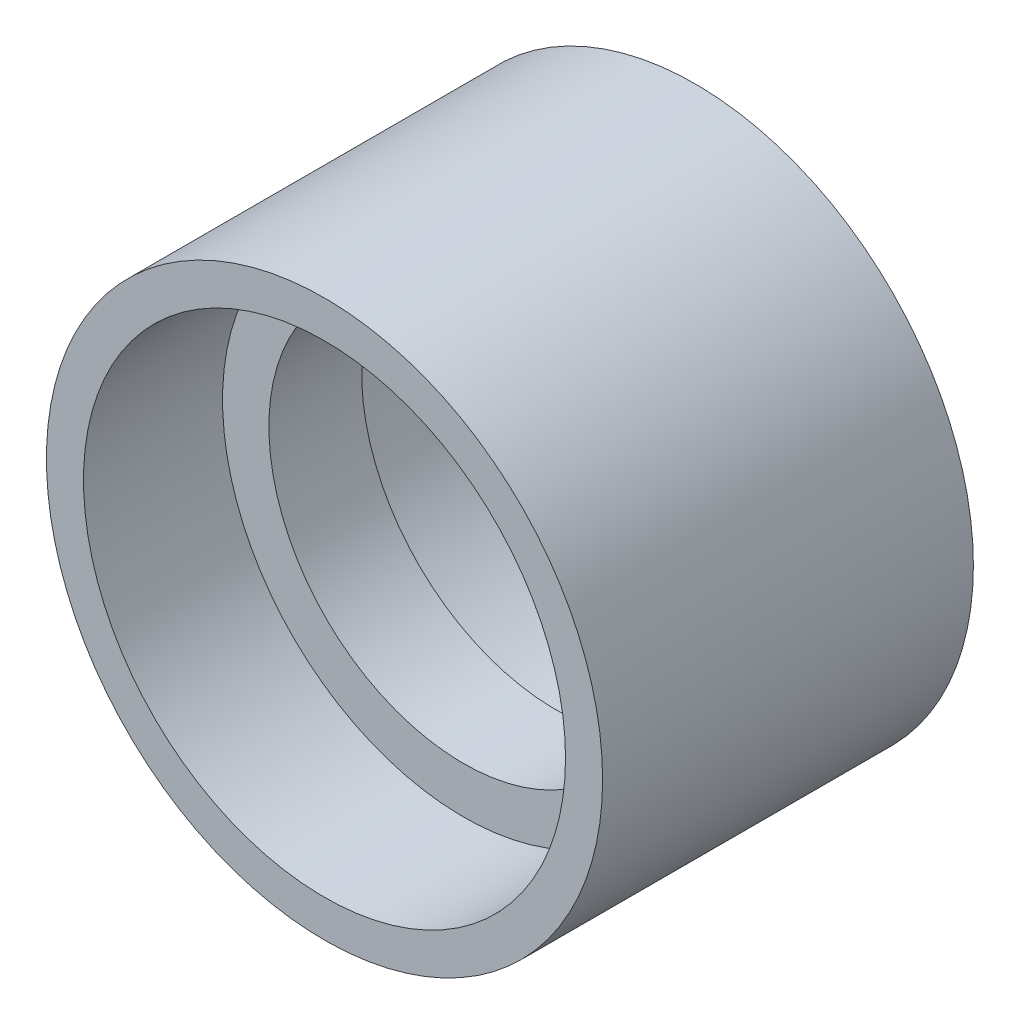
SolidWorks part; units mm, degrees
material "AISI 1020"
ref_plane "Спереди" through (0, 0, 0) normal (0, 0, 1) x (1, 0, 0)
ref_plane "Сверху" through (0, 0, 0) normal (0, 1, 0) x (1, 0, 0)
ref_plane "Справа" through (0, 0, 0) normal (1, 0, 0) x (0, 0, -1)
sketch "Эскиз1" plane through (0, 0, 0) normal (1, 0, 0) x (0, 0, -1)
  line L0 (-1000, 0) -> (49000, 0) construction
  line L1 (20, 30) -> (20, 26)
  line L2 (20, -230.3984) -> (20, 198.7465) construction
  line L3 (20, 26) -> (5, 26)
  line L4 (5, 26) -> (5, 21)
  line L5 (5, 21) -> (0, 21)
  line L6 (0, -224.6674) -> (0, -114.6674) construction
  line L7 (0, 21) -> (0, 30)
  line L8 (0, 30) -> (20, 30)
  line L9 (5, 24.5) -> (5, -24.5) construction
  line L10 (18.5, 26) -> (6.5, 26) construction
  line L11 (7.5, 21) -> (5, 21) construction
revolve "Повернуть1" add sketch "Эскиз1" angle 360 about L0
mirror "Зеркальное отражение1" about plane through (0, 21, 0) normal (0, 0, -1) of bodies 103
